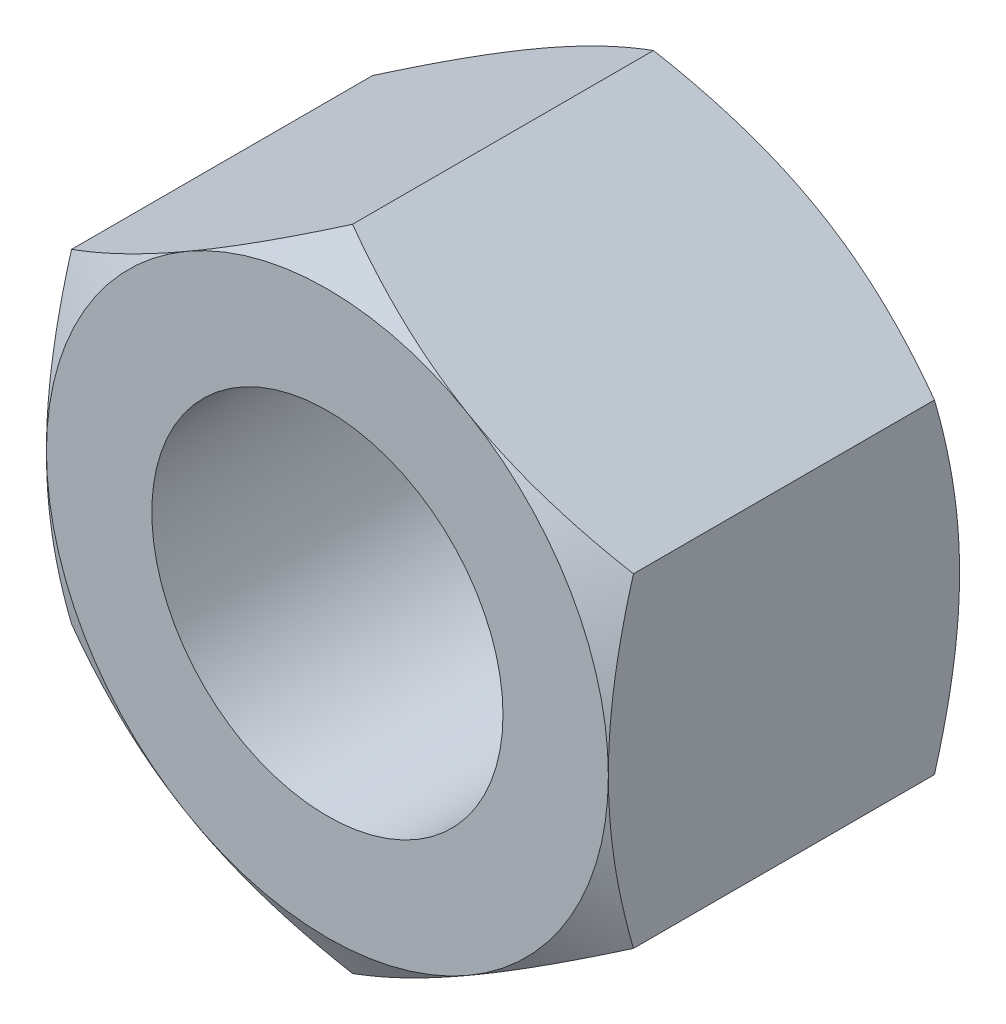
SolidWorks part; units mm, degrees
ref_plane "Plan de face" through (0, 0, 0) normal (0, 0, 1) x (1, 0, 0)
ref_plane "Plan de dessus" through (0, 0, 0) normal (0, 1, 0) x (1, 0, 0)
ref_plane "Plan de droite" through (0, 0, 0) normal (1, 0, 0) x (0, 0, -1)
sketch "Esquisse1" plane through (0, 0, 0) normal (0, 0, 1) x (1, 0, 0)
  line L1 (0, 4.6188) -> (-4, 2.3094)
  line L2 (-4, 2.3094) -> (-4, -2.3094)
  line L3 (-4, -2.3094) -> (0, -4.6188)
  line L4 (0, -4.6188) -> (4, -2.3094)
  line L5 (4, -2.3094) -> (4, 2.3094)
  line L6 (4, 2.3094) -> (0, 4.6188)
  circle A0 centre (0, 0) radius 4 construction
  dimension "D1" = 8
extrude "Boss.-Extru.1" add sketch "Esquisse1" along normal blind 5
sketch "Esquisse2" plane through (0, 0, 5) normal (0, 0, 1) x (1, 0, 0)
  circle A0 centre (0, 0) radius 2.5
  dimension "D1" = 5
extrude "Enlèv. mat.-Extru.1" cut sketch "Esquisse2" against normal up to next
sketch "Esquisse4" plane through (0, 0, 0) normal (0, 1, 0) x (1, 0, 0)
  line L0 (-8.3301, -2.5) -> (-2.2679, 1)
  line L1 (0, 0) -> (-4, 0) construction
  line L3 (-8.3301, -2.5) -> (-2.2679, -6)
  line L4 (-2.2679, 1) -> (-9.3301, 1)
  line L5 (-9.3301, 1) -> (-9.3301, -6)
  line L6 (-9.3301, -6) -> (-2.2679, -6)
  line L7 (0, 0) -> (0, -5) construction
  dimension "D1" = 1
  dimension "D2" = 1
  dimension "D3" = 30
revolve "Enlèvement de matière-Révolution8" cut sketch "Esquisse4" angle 360 about L7
